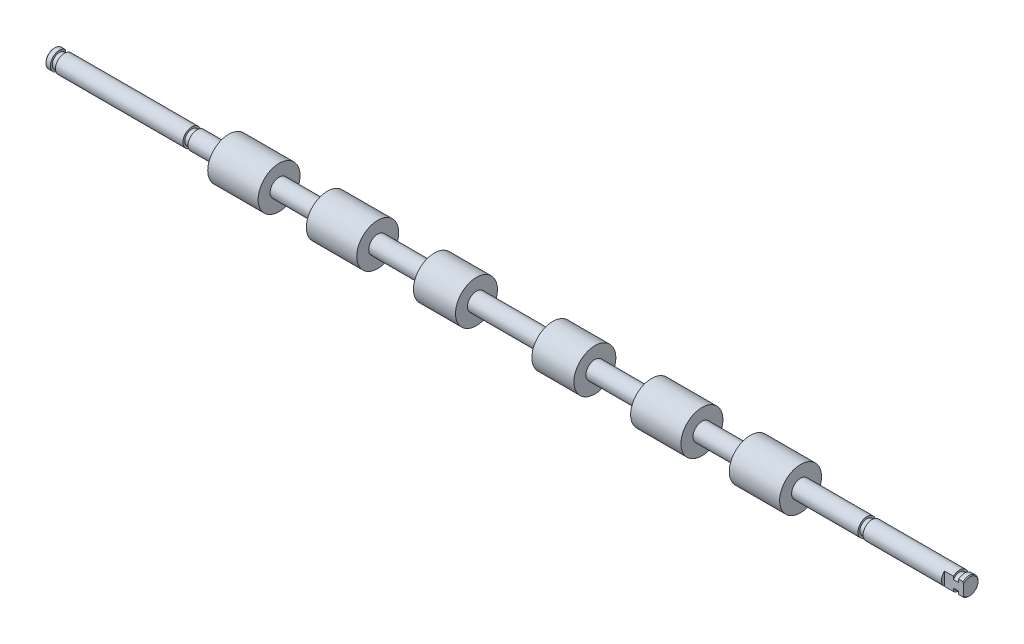
SolidWorks part; units mm, degrees
ref_plane "Face" through (0, 0, 0) normal (0, 0, 1) x (1, 0, 0)
ref_plane "Dessus" through (0, 0, 0) normal (0, 1, 0) x (1, 0, 0)
ref_plane "Droite" through (0, 0, 0) normal (1, 0, 0) x (0, 0, -1)
sketch "Esquisse1" plane through (0, 0, 0) normal (0, 0, 1) x (1, 0, 0)
  line L0 (0, 0) -> (305.3, 0) construction
  line L1 (0, 0) -> (0, 2.975)
  line L2 (0, 2.975) -> (1.7, 2.975)
  line L3 (1.7, 2.975) -> (1.7, 2.35)
  line L4 (1.7, 2.35) -> (3.4, 2.35)
  line L5 (3.4, 2.35) -> (3.4, 2.975)
  line L6 (3.4, 2.975) -> (45.65, 2.975)
  line L7 (45.65, 2.975) -> (45.65, 2.35)
  line L8 (45.65, 2.35) -> (47.35, 2.35)
  line L9 (47.35, 2.35) -> (47.35, 2.975)
  line L10 (47.35, 2.975) -> (57.85, 2.975)
  line L11 (57.85, 2.975) -> (57.85, 6.95)
  line L12 (57.85, 6.95) -> (74.55, 6.95)
  line L13 (74.55, 6.95) -> (74.55, 2.975)
  line L14 (74.55, 2.975) -> (90.55, 2.975)
  line L15 (90.55, 2.975) -> (90.55, 6.95)
  line L16 (90.55, 6.95) -> (107.25, 6.95)
  line L17 (107.25, 6.95) -> (107.25, 2.975)
  line L18 (107.25, 2.975) -> (126.05, 2.975)
  line L19 (126.05, 2.975) -> (126.05, 6.95)
  line L20 (126.05, 6.95) -> (140, 6.95)
  line L21 (140, 6.95) -> (140, 2.975)
  line L22 (140, 2.975) -> (165.3, 2.975)
  line L23 (152.65, 0) -> (152.65, 2.975) construction
  line L24 (152.65, 2.975) -> (305.3, 2.975) construction
  line L25 (305.3, 2.975) -> (305.3, 0) construction
  line L26 (247.45, 2.975) -> (247.45, 6.95)
  line L27 (247.45, 6.95) -> (230.75, 6.95)
  line L28 (230.75, 6.95) -> (230.75, 2.975)
  line L29 (230.75, 2.975) -> (214.75, 2.975)
  line L30 (214.75, 2.975) -> (214.75, 6.95)
  line L31 (214.75, 6.95) -> (198.05, 6.95)
  line L32 (198.05, 6.95) -> (198.05, 2.975)
  line L33 (198.05, 2.975) -> (179.25, 2.975)
  line L34 (179.25, 2.975) -> (179.25, 6.95)
  line L35 (179.25, 6.95) -> (165.3, 6.95)
  line L36 (165.3, 6.95) -> (165.3, 2.975)
  line L37 (247.45, 2.975) -> (269.45, 2.975)
  line L38 (269.45, 2.975) -> (269.45, 2.35)
  line L39 (269.45, 2.35) -> (271.15, 2.35)
  line L40 (271.15, 2.35) -> (271.15, 2.975)
  line L41 (271.15, 2.975) -> (300.15, 2.975)
  line L42 (300.15, 2.975) -> (300.15, 2.35)
  line L43 (300.15, 2.35) -> (301.85, 2.35)
  line L44 (301.85, 2.35) -> (301.85, 2.975)
  line L45 (301.85, 2.975) -> (303.55, 2.975)
  line L46 (303.55, 2.975) -> (303.55, 0)
  line L47 (0, 0) -> (303.55, 0)
  dimension "D1" = 16.7
  dimension "D2" = 13.95
  dimension "D3" = 13.9
  dimension "D4" = 5.95
  dimension "D5" = 4.7
  dimension "D6" = 1.7
  dimension "D7" = 16
  dimension "D8" = 18.8
  dimension "D9" = 12.65
  dimension "D10" = 10.5
  dimension "D11" = 45.65
  dimension "D12" = 1.7
  dimension "D13" = 1.7
  dimension "D14" = 22
  dimension "D15" = 32.4
revolve "Révolution1" add sketch "Esquisse1" angle 360 about L47
sketch "Esquisse2" plane through (0, 0, 0) normal (0, 1, 0) x (1, 0, 0)
  line L0 (3.4, -2.975) -> (45.65, -2.975) construction
  line L1 (0, 4.7937) -> (16.4, 4.7937)
  line L2 (0, 4.7937) -> (0, 2.005)
  line L3 (0, 2.005) -> (16.4, 2.005)
  line L4 (16.4, 4.7937) -> (16.4, 2.005)
  line L5 (0, 2.975) -> (0, -2.975) construction
  line L6 (300.15, 2.975) -> (271.15, 2.975) construction
  line L7 (305.8477, -4.9042) -> (297.15, -4.9042)
  line L8 (305.8477, -4.9042) -> (305.8477, -2.005)
  line L9 (305.8477, -2.005) -> (297.15, -2.005)
  line L10 (297.15, -4.9042) -> (297.15, -2.005)
  line L11 (303.55, -2.975) -> (303.55, 2.975) construction
  line L12 (15.4, -1.5707) -> (15.4, 1.5707) construction
  line L13 (15.4, -1.5707) -> (15.4, 1.5707) construction
  dimension "D1" = 4.98
  dimension "D2" = 1
  dimension "D3" = 4.98
  dimension "D4" = 6.4
  dimension "D5" = 2.7887
extrude "Enlèv. mat.-Extru.1" cut sketch "Esquisse2" against normal through all and the other way through all
chamfer "Chanfrein1" distance 0.25 angle 45 2 edges at (0, 0, 2.975) (303.55, 0, -2.975)
ref_plane "Plan1" through (152.65, 0, 0) normal (1, 0, 0) x (0, 0, -1)
